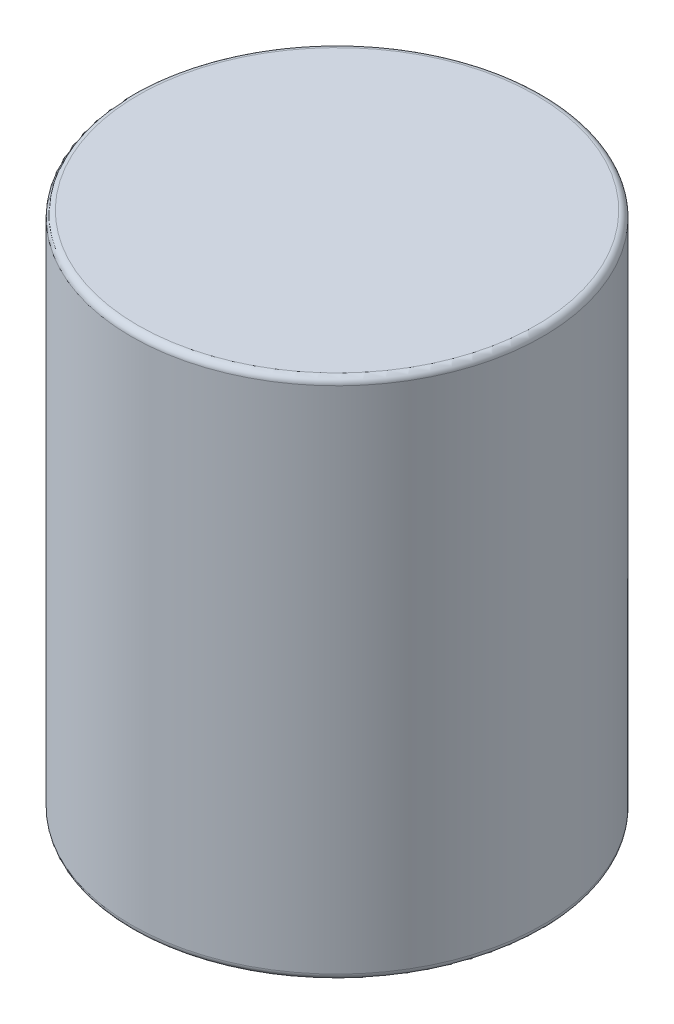
SolidWorks part; units mm, degrees
ref_plane "Спереди" through (0, 0, 0) normal (0, 0, 1) x (1, 0, 0)
ref_plane "Сверху" through (0, 0, 0) normal (0, 1, 0) x (1, 0, 0)
ref_plane "Справа" through (0, 0, 0) normal (1, 0, 0) x (0, 0, -1)
sketch "Эскиз1" plane through (0, 0, 0) normal (0, 1, 0) x (1, 0, 0)
  circle A0 centre (0, 0) radius 3.15
  dimension "D1" = 6.3
extrude "Бобышка-Вытянуть1" add sketch "Эскиз1" along normal blind 8
fillet "Скругление1" radius 0.1 1 edges at (0, 8, 3.15)
fillet "Скругление2" radius 0.1 1 edges at (0, 0, 3.15)
